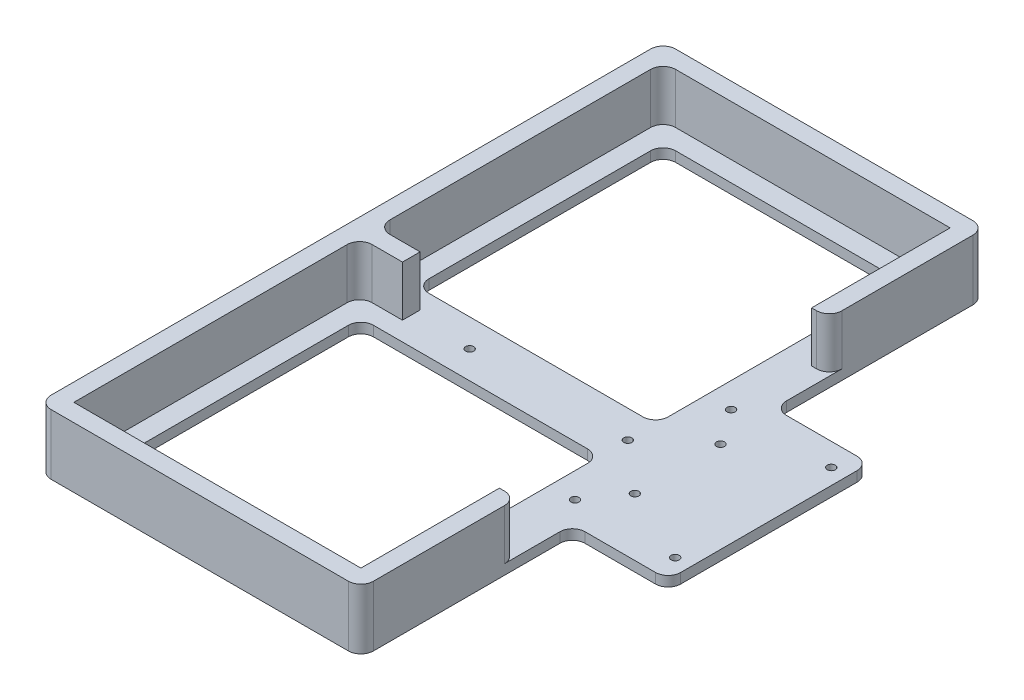
SolidWorks part; units mm, degrees
ref_plane "Front Plane" through (0, 0, 0) normal (0, 0, 1) x (1, 0, 0)
ref_plane "Top Plane" through (0, 0, 0) normal (0, 1, 0) x (1, 0, 0)
ref_plane "Right Plane" through (0, 0, 0) normal (1, 0, 0) x (0, 0, -1)
sketch "Sketch1" plane through (0, 0, 0) normal (0, 1, 0) x (1, 0, 0)
  line L0 (-62.8, 0) -> (0, 0) construction
  line L1 (0, 0) -> (0, 50000) construction
  line L2 (10, 31) -> (49.8, 31) construction
  line L3 (10, -31) -> (49.8, -31) construction
  line L4 (0, 11) -> (-95, 11)
  line L6 (0, 11) -> (0, 40)
  line L7 (18, 40) -> (56, 40)
  line L8 (56, 40) -> (56, -40)
  line L9 (0, -11) -> (0, -40)
  line L10 (18, -40) -> (56, -40)
  line L11 (0, -11) -> (-95, -11)
  line L12 (-95, 11) -> (-95, 109)
  line L13 (-95, 109) -> (0, 109)
  line L14 (0, 109) -> (0, 40)
  line L15 (18, 40) -> (18, 124)
  line L16 (18, 124) -> (-110, 124)
  line L17 (-110, 124) -> (-110, 22.9046)
  line L18 (0, -109) -> (0, -40)
  line L19 (18, -40) -> (18, -124)
  line L20 (18, -124) -> (-110, -124)
  line L21 (-95, -109) -> (0, -109)
  line L22 (-95, -11) -> (-95, -109)
  line L23 (-110, -124) -> (-110, -22.9046)
  line L24 (-110, 22.9046) -> (-110, -22.9046)
  line L25 (-20.1555, 92) -> (-79.1555, 92) construction
  line L26 (-79.1555, -92) -> (-20.1555, -92) construction
  line L27 (0, 0) -> (-50000, 0) construction
  circle A0 centre (0, 0) radius 1.6
  circle A1 centre (-62.8, 0) radius 1.6
  circle A2 centre (10, 31) radius 1.6
  circle A3 centre (49.8, 31) radius 1.6
  circle A4 centre (49.8, -31) radius 1.6
  circle A5 centre (10, -31) radius 1.6
  circle A6 centre (19.8, 17) radius 1.6
  circle A7 centre (19.8, -17) radius 1.6
  point P22 (56, 0)
  point P25 (-95, 0)
  dimension "D1" = 3.2
  dimension "D2" = 3.2
  dimension "D6" = 3.2
  dimension "D7" = 3.2
  dimension "D19" = 3.2
  dimension "D20" = 3.2
  dimension "D3" = 62.8
  dimension "D4" = 10
  dimension "D5" = 31
  dimension "D8" = 39.8
  dimension "D9" = 22
  dimension "D10" = 80
  dimension "D11" = 56
  dimension "D12" = 95
  dimension "D13" = 18
  dimension "D14" = 15
  dimension "D15" = 15
  dimension "D16" = 15
  dimension "D17" = 17
  dimension "D18" = 17
extrude "Boss-Extrude1" add sketch "Sketch1" along normal mid plane 4
sketch "Sketch2" plane through (0, 2, 0) normal (0, 1, 0) x (1, 0, 0)
  line L0 (18, 124) -> (-110, 124)
  line L1 (-110, 124) -> (-110, -124)
  line L2 (-110, 124) -> (-110, -124) construction
  line L5 (-103, 117) -> (11, 117)
  line L6 (18, 40) -> (18, 124) construction
  line L7 (18, 117) -> (18, 124)
  line L8 (0, 0) -> (50000, 0) construction
  line L9 (18, -117) -> (18, -124)
  line L11 (18, -124) -> (-110, -124)
  line L12 (-103, 117) -> (-103, 3.5)
  line L13 (-103, 3.5) -> (-86, 3.5)
  line L14 (-86, 3.5) -> (-86, -3.5)
  line L15 (-103, -3.5) -> (-86, -3.5)
  line L16 (-103, -117) -> (-103, -3.5)
  line L17 (18, 117) -> (18, 62)
  line L18 (18, 62) -> (11, 62)
  line L19 (11, 62) -> (11, 117)
  line L20 (56, 40) -> (18, 40) construction
  line L21 (18, -62) -> (11, -62)
  line L22 (18, -117) -> (18, -62)
  line L23 (11, -62) -> (11, -117)
  line L24 (-103, -117) -> (11, -117)
  point P19 (-103, 0)
  point P20 (-110, 0)
  point P24 (-86, 0)
  dimension "D2" = 7
  dimension "D1" = 7
  dimension "D3" = 17
  dimension "D4" = 7
  dimension "D5" = 7
  dimension "D6" = 22
extrude "Boss-Extrude2" add sketch "Sketch2" along normal blind 20
fillet "Fillet1" radius 5 21 edges at (56, 0, -40) (56, 0, 40) (18, 0, -40) (18, 0, 40) (18, 10, -124) (18, 10, 124) (-110, 10, -124) (0, 0, -109) (0, 0, -11) (-103, 12, -117) (-95, 0, -109) (-95, 0, -11) (0, 0, 109) (0, 0, 11) (-103, 12, -3.5) (-103, 12, 3.5) (-95, 0, 11) (-95, 0, 109) (-110, 10, 124) (18, 12, -62) (18, 12, 62)
equation "\"D2@Sketch1\"=\"D1@Sketch1\""
equation "\"D6@Sketch1\"=\"D2@Sketch1\""
equation "\"D7@Sketch1\"=\"D2@Sketch1\""
equation "\"D2@Sketch2\"=\"D5@Sketch2\""
equation "\"D15@Sketch1\"=\"D14@Sketch1\""
equation "\"D4@Sketch2\"=\"D5@Sketch2\""
